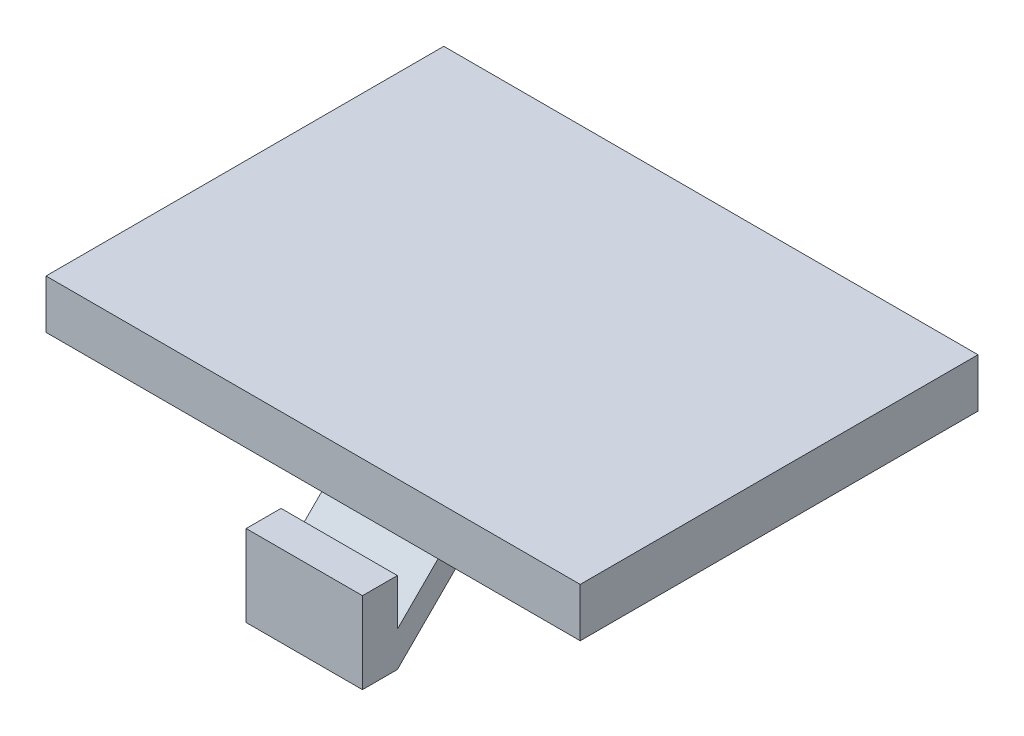
SolidWorks part; units mm, degrees
ref_plane "Alzado" through (0, 0, 0) normal (0, 0, 1) x (1, 0, 0)
ref_plane "Planta" through (0, 0, 0) normal (0, 1, 0) x (1, 0, 0)
ref_plane "Vista lateral" through (0, 0, 0) normal (1, 0, 0) x (0, 0, -1)
sketch "Croquis1" plane through (0, 0, 0) normal (0, 0, 1) x (1, 0, 0)
  line L1 (0, 0) -> (-184, 0)
  line L2 (0, 0) -> (0, 39)
  line L3 (0, 39) -> (-184, 39)
  line L4 (-184, 0) -> (-184, 39)
  dimension "D1" = 184
  dimension "D2" = 39
extrude "Saliente-Extruir1" add sketch "Croquis1" along normal blind 17.1
sketch "Croquis3" plane through (0, 0, 17.1) normal (0, 0, 1) x (1, 0, 0)
  line L8 (-2.1, 2.1) -> (-2.1, 36.9)
  line L9 (-2.1, 36.9) -> (-181.9, 36.9)
  line L10 (-181.9, 36.9) -> (-181.9, 2.1)
  line L11 (-181.9, 2.1) -> (-2.1, 2.1)
  line L12 (-2.1, 2.1) -> (-2.1, 36.9)
  line L13 (-2.1, 36.9) -> (-181.9, 36.9)
  line L14 (-181.9, 36.9) -> (-181.9, 2.1)
  line L15 (-181.9, 2.1) -> (-2.1, 2.1)
  dimension "D1" = 2.1
extrude "Cortar-Extruir2" cut sketch "Croquis3" against normal blind 5
sketch "Croquis2" plane through (0, 0, 12.1) normal (0, 0, 1) x (1, 0, 0)
  line L0 (-105.9, 34.7) -> (-105.9, 36.2)
  line L1 (-8.9, 34.7) -> (-95.9, 34.7)
  line L3 (-8.9, 17.7) -> (-17.9, 17.7)
  line L4 (-108.9, 34.7) -> (-108.9, 33.7)
  line L5 (-172.7, 4.1) -> (-172.7, 2.1) construction
  line L6 (-23.9, 17.7) -> (-64.1099, 17.7)
  line L8 (-23.9, 17.7) -> (-23.9, 15.7)
  line L9 (-23.9, 15.7) -> (-17.9, 15.7)
  line L10 (-17.9, 17.7) -> (-17.9, 15.7)
  line L11 (-91.9, 17.7) -> (-108.9, 17.7)
  line L13 (-91.9, 17.7) -> (-91.9, 16.8)
  line L16 (-105.9, 36.2) -> (-95.9, 36.2)
  line L17 (-108.9, 33.7) -> (-179.9, 33.7)
  line L19 (-108.9, 22.7) -> (-127.3778, 22.7)
  line L20 (-179.9, 33.7) -> (-179.9, 22.7)
  line L21 (-108.9, 22.7) -> (-108.9, 17.7)
  line L23 (-136.1099, 16.8) -> (-91.9, 16.8)
  line L24 (-136.1099, 16.8) -> (-136.1099, 14.2)
  line L25 (-136.1099, 5.8) -> (-64.1099, 5.8)
  line L26 (-64.1099, 17.7) -> (-64.1099, 5.8)
  line L27 (-95.9, 36.2) -> (-95.9, 34.7)
  line L28 (-52.1, 7.6) -> (-4.1, 7.6)
  line L29 (-52.1, 7.6) -> (-52.1, 5.8)
  line L30 (-52.1, 5.8) -> (-4.1, 5.8)
  line L31 (-4.1, 7.6) -> (-4.1, 5.8)
  line L35 (-166.1099, 14.2) -> (-136.1099, 14.2)
  line L37 (-166.1099, 8.4) -> (-136.1099, 8.4)
  line L39 (-105.9, 34.7) -> (-108.9, 34.7)
  line L40 (-136.1099, 8.4) -> (-136.1099, 5.8)
  line L41 (-147.1, 14.7) -> (-147.1, 14.2) construction
  line L42 (-181.9, 36.9) -> (-181.9, 2.1) construction
  line L43 (-2.1, 2.1) -> (-2.1, 36.9) construction
  line L44 (-181.9, 2.1) -> (-2.1, 2.1) construction
  line L45 (-3.7, 26.2) -> (-2.1, 26.2) construction
  line L46 (-147.1, 14.7) -> (-147.1, 33.7) construction
  line L47 (-166.8222, 22.7) -> (-179.9, 22.7)
  line L48 (-179.9, 11.3) -> (-181.9, 11.3) construction
  line L51 (-26.8099, 9.9) -> (-61.8099, 9.9)
  line L52 (-26.8099, 9.9) -> (-26.8099, 15.4)
  line L53 (-26.8099, 15.4) -> (-61.8099, 15.4)
  line L54 (-61.8099, 9.9) -> (-61.8099, 15.4)
  arc A0 (-166.1099, 8.4) -> (-166.1099, 14.2) centre (-172.7, 11.3) cw
  arc A1 (-8.9, 34.7) -> (-8.9, 17.7) centre (-13.2471, 26.2) cw
  arc A2 (-166.8222, 22.7) -> (-127.3778, 22.7) centre (-147.1, 43.0103) ccw
  circle A3 centre (-12.6817, 9.8002) radius 0.8
  circle A4 centre (-6.6825, 9.7004) radius 0.8
  dimension "D29" = 1.6
  dimension "D30" = 6
  dimension "D31" = 2.3
  dimension "D1" = 17
  dimension "D3" = 2
  dimension "D4" = 100
  dimension "D5" = 19
  dimension "D6" = 6
  dimension "D7" = 2
  dimension "D8" = 17
  dimension "D9" = 3
  dimension "D10" = 11
  dimension "D11" = 71
  dimension "D12" = 1
  dimension "D13" = 11
  dimension "D14" = 72
  dimension "D15" = 0.5
  dimension "D16" = 48
  dimension "D17" = 2
  dimension "D18" = 1.8
  dimension "D19" = 9
  dimension "D20" = 2
  dimension "D21" = 5.8
  dimension "D22" = 30
  dimension "D23" = 2
  dimension "D24" = 44.2099
  dimension "D25" = 2.6
  dimension "D26" = 1.6
  dimension "D27" = 1.5
  dimension "D28" = 10
  dimension "D32" = 2.3
  dimension "D33" = 2.3
  dimension "D34" = 35
extrude "Cortar-Extruir1" cut sketch "Croquis2" against normal blind 10 from surface at 0 starting at face at (-92, 19.5, 12.1)
sketch "Croquis4" plane through (-184, 0, 0) normal (-1, 0, 0) x (0, 0, 1)
  line L0 (17.1, 40.5) -> (17.1, 39)
  line L1 (17.1, 39) -> (17.1, 0) construction
  line L3 (12.1, 45.5) -> (12.1, 39)
  line L4 (17.1, 39) -> (0, 39) construction
  line L5 (17.1, 39) -> (12.1, 39)
  circle A0 centre (17.1, 45.5) radius 1.7
  circle A1 centre (17.1, 45.5) radius 3 construction
  arc A2 (17.1, 40.5) -> (12.1, 45.5) centre (17.1, 45.5) ccw
  dimension "D1" = 3.4
  dimension "D2" = 10
  dimension "D3" = 6
  dimension "D4" = 1.5
extrude "Saliente-Extruir2" add sketch "Croquis4" against normal blind 10 from offset 30 separate body offset against normal yes
sketch "Croquis5" plane through (-154, 0, 0) normal (-1, 0, 0) x (0, 0, 1)
  circle A0 centre (17.1, 45.5) radius 3
  dimension "D1" = 6
extrude "Cortar-Extruir3" cut sketch "Croquis5" against normal blind 2
ref_plane "Plano1" through (-92, 0, 0) normal (-1, 0, 0) x (0, 0, 1)
mirror "Simetría1" about plane through (-92, 0, 0) normal (-1, 0, 0) of bodies 105
fillet "Redondeo1" radius 3 8 edges at (-2.1, 2.1, 14.6) (-2.1, 36.9, 14.6) (-181.9, 2.1, 14.6) (-181.9, 36.9, 14.6) (0, 39, 8.55) (0, 0, 8.55) (-184, 39, 8.55) (-184, 0, 8.55)
sketch "Croquis6" plane through (-184, 0, 0) normal (-1, 0, 0) x (0, 0, 1)
  line L0 (12.6, 0) -> (11.1, 0)
  line L1 (17.1, 0) -> (0, 0) construction
  line L3 (16.6, -5.5) -> (18.1, -5.5)
  line L4 (18.1, -5.5) -> (18.1, -2)
  line L5 (18.1, -2) -> (16.6, -2)
  line L6 (16.6, -2) -> (16.6, -4)
  line L13 (12.6, 0) -> (16.6, -4)
  line L14 (11.1, 0) -> (16.6, -5.5)
  line L15 (17.1, 0) -> (17.1, 3) construction
  dimension "D1" = 4.5
  dimension "D2" = 1.5
  dimension "D3" = 2
  dimension "D4" = 2
  dimension "D5" = 1.5
  dimension "D6" = 1.5
  dimension "D7" = 1
extrude "Saliente-Extruir3" add sketch "Croquis6" along normal blind 2.5 and the other way blind 2.5 from surface at -92 separate body starting at plane "Plano1"
sketch "Croquis7" plane through (0, 0, 17.1) normal (0, 0, 1) x (1, 0, 0)
  line L0 (-178.9, 2.1) -> (-5.1, 2.1) construction
  line L1 (-104.1038, 2.1) -> (-81.1401, 2.1)
  line L2 (-104.1038, 2.1) -> (-104.1038, -8.8041)
  line L4 (-81.1401, 2.1) -> (-81.1401, -8.8041)
  line L5 (-104.1038, -8.8041) -> (-195.2516, -7.5005)
  line L6 (-195.2516, -7.5005) -> (-194.2079, 65.4724)
  line L7 (-194.2079, 65.4724) -> (14.7356, 62.484)
  line L8 (14.7356, 62.484) -> (14.7356, -8.8041)
  line L9 (14.7356, -8.8041) -> (-81.1401, -8.8041)
extrude "Cortar-Extruir4" cut sketch "Croquis7" against normal up to vertex (17.1 mm away) and the other way blind 10
